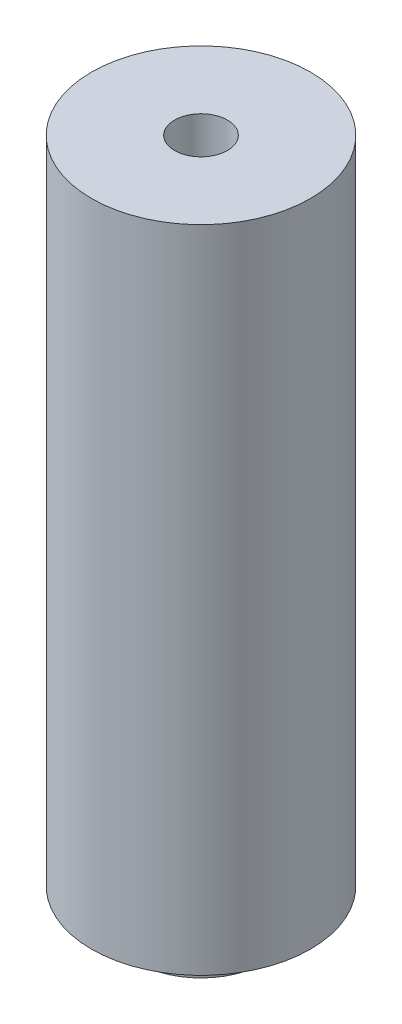
SolidWorks part; units mm, degrees
ref_plane "Front Plane" through (0, 0, 0) normal (0, 0, 1) x (1, 0, 0)
ref_plane "Top Plane" through (0, 0, 0) normal (0, 1, 0) x (1, 0, 0)
ref_plane "Right Plane" through (0, 0, 0) normal (1, 0, 0) x (0, 0, -1)
sketch "Sketch1" plane through (0, 0, 0) normal (0, 1, 0) x (1, 0, 0)
  circle A0 centre (0, 0) radius 4
  circle A1 centre (0, 0) radius 0.965
  dimension "D1" = 8
  dimension "D2" = 1.93
extrude "Boss-Extrude1" add sketch "Sketch1" along normal blind 25
sketch "Sketch2" plane through (0, 0, 0) normal (0, -1, 0) x (1, 0, 0)
  circle A0 centre (0, 0) radius 2.35
  circle A1 centre (0, 0) radius 4 construction
  circle A2 centre (0, 0) radius 4
  dimension "D1" = 4.7
extrude "Cut-Extrude1" cut sketch "Sketch2" against normal blind 1.25
